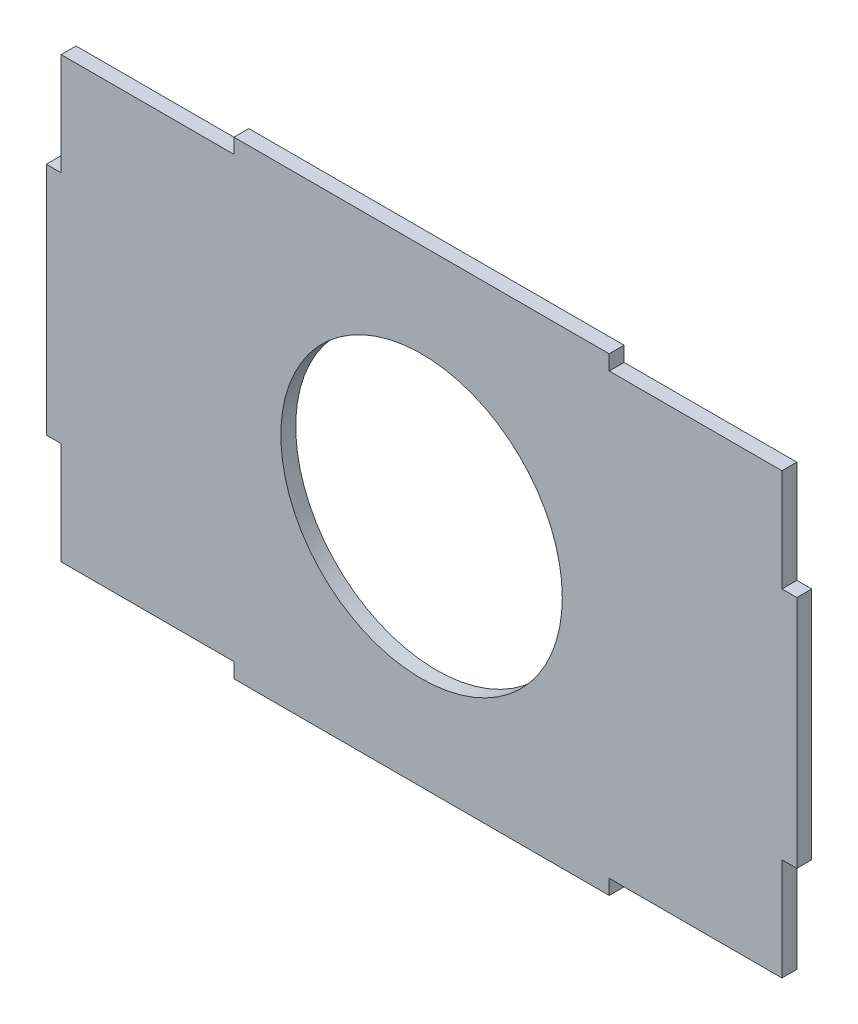
SolidWorks part; units mm, degrees
ref_plane "Front Plane" through (0, 0, 0) normal (0, 0, 1) x (1, 0, 0)
ref_plane "Top Plane" through (0, 0, 0) normal (0, 1, 0) x (1, 0, 0)
ref_plane "Right Plane" through (0, 0, 0) normal (1, 0, 0) x (0, 0, -1)
sketch "Sketch1" plane through (0, 0, 0) normal (0, 0, 1) x (1, 0, 0)
  line L0 (-214.0676, 0) -> (265.1603, 0) construction
  line L1 (0, 140.7848) -> (0, -166.5177) construction
  line L2 (-40, 0) -> (40, 0)
  line L3 (40, 0) -> (40, 3.175)
  line L4 (40, 3.175) -> (76.825, 3.175)
  line L5 (76.825, 3.175) -> (76.825, 25)
  line L6 (76.825, 25) -> (80, 25)
  line L7 (80, 25) -> (80, 75)
  line L8 (80, 75) -> (76.825, 75)
  line L9 (76.825, 75) -> (76.825, 96.825)
  line L10 (76.825, 96.825) -> (40, 96.825)
  line L11 (40, 96.825) -> (40, 100)
  line L12 (40, 100) -> (-40, 100)
  line L13 (-40, 96.825) -> (-40, 100)
  line L14 (-76.825, 96.825) -> (-40, 96.825)
  line L15 (-76.825, 75) -> (-76.825, 96.825)
  line L16 (-80, 75) -> (-76.825, 75)
  line L17 (-80, 25) -> (-80, 75)
  line L18 (-76.825, 25) -> (-80, 25)
  line L19 (-76.825, 3.175) -> (-76.825, 25)
  line L20 (-40, 3.175) -> (-76.825, 3.175)
  line L21 (-40, 0) -> (-40, 3.175)
  point P18 (0, 0)
  point P19 (0, 100)
  dimension "D1" = 40
  dimension "D2" = 3.175
  dimension "D3" = 36.825
  dimension "D4" = 21.825
  dimension "D5" = 3.175
  dimension "D6" = 50
  dimension "D7" = 3.175
  dimension "D8" = 21.825
  dimension "D9" = 36.825
  dimension "D10" = 3.175
extrude "Boss-Extrude2" add sketch "Sketch1" along normal blind 3.175
sketch "Sketch2" plane through (0, 0, 3.175) normal (0, 0, 1) x (1, 0, 0)
  line L0 (-96.2522, 50) -> (109.8222, 50) construction
  line L1 (-40, 0) -> (40, 0) construction
  line L2 (0, -9.5839) -> (0, 126.7513) construction
  circle A0 centre (0, 50) radius 30
  dimension "D1" = 50
extrude "Cut-Extrude1" cut sketch "Sketch2" against normal blind 3.175
